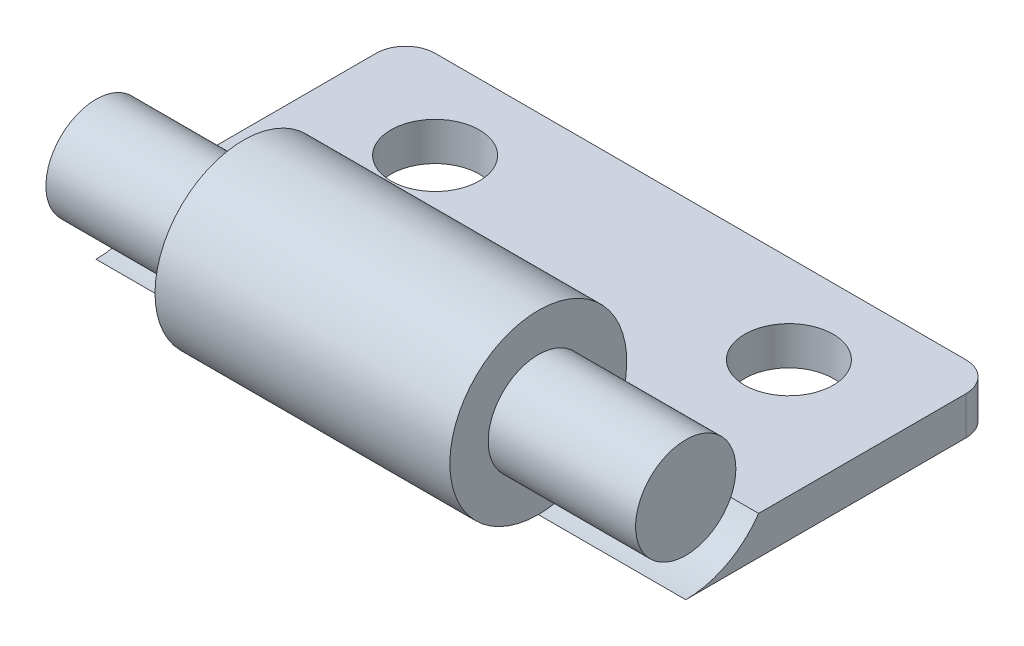
SolidWorks part; units mm, degrees
ref_plane "前视基准面" through (0, 0, 0) normal (0, 0, 1) x (1, 0, 0)
ref_plane "上视基准面" through (0, 0, 0) normal (0, 1, 0) x (1, 0, 0)
ref_plane "右视基准面" through (0, 0, 0) normal (1, 0, 0) x (0, 0, -1)
sketch "草图1" plane through (0, 0, 0) normal (1, 0, 0) x (0, 0, -1)
  line L1 (0, 0) -> (10.5, 0)
  line L2 (0, 0) -> (0, 1.3)
  line L3 (0, 1.3) -> (10.5, 1.3)
  line L4 (10.5, 0) -> (10.5, 1.3)
extrude "凸台-拉伸1" add sketch "草图1" along normal mid plane 20
sketch "草图2" plane through (10, 0, 0) normal (1, 0, 0) x (0, 0, -1)
  circle A0 centre (0, 3) radius 3
extrude "切除-拉伸1" cut sketch "草图2" against normal blind 5
sketch "草图3" plane through (5, 0, 0) normal (1, 0, 0) x (0, 0, -1)
  circle A0 centre (0, 3) radius 3
extrude "凸台-拉伸2" add sketch "草图3" against normal blind 10
sketch "草图4" plane through (5, 0, 0) normal (1, 0, 0) x (0, 0, -1)
  circle A0 centre (0, 3) radius 1.7
extrude "凸台-拉伸3" add sketch "草图4" along normal blind 5
mirror "镜向1" about plane through (0, 0, 0) normal (1, 0, 0) of "切除-拉伸1", "凸台-拉伸3"
sketch "草图5" plane through (0, 1.3, 0) normal (0, 1, 0) x (1, 0, 0)
  line L0 (10, 10.5) -> (-10, 10.5) construction
  line L1 (-10, 10.5) -> (-10, 2.4718) construction
  circle A0 centre (-6, 7.5) radius 1.5
  dimension "D1" = 3
  dimension "D2" = 4
extrude "切除-拉伸2" cut sketch "草图5" against normal blind 5
mirror "镜向2" about plane through (0, 0, 0) normal (1, 0, 0) of "切除-拉伸2"
fillet "圆角1" radius 1 2 edges at (-10, 0.65, -10.5) (10, 0.65, -10.5)
